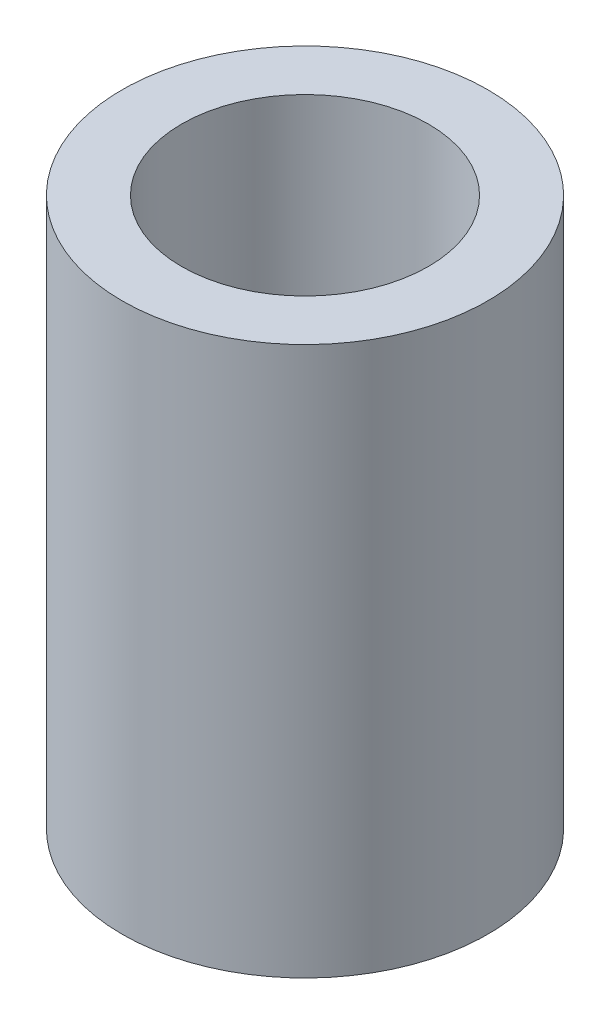
SolidWorks part; units mm, degrees
ref_plane "Front Plane" through (0, 0, 0) normal (0, 0, 1) x (1, 0, 0)
ref_plane "Top Plane" through (0, 0, 0) normal (0, 1, 0) x (1, 0, 0)
ref_plane "Right Plane" through (0, 0, 0) normal (1, 0, 0) x (0, 0, -1)
sketch "Sketch1" plane through (0, 0, 0) normal (0, 1, 0) x (1, 0, 0)
  circle A0 centre (0, 0) radius 5
extrude "Boss-Extrude2" add sketch "Sketch1" along normal blind 15 contours A0
sketch "Sketch2" plane through (0, 0, 0) normal (0, 1, 0) x (1, 0, 0)
  circle A0 centre (0, 0) radius 3.375
extrude "Cut-Extrude1" cut sketch "Sketch2" along normal through all contours A0
